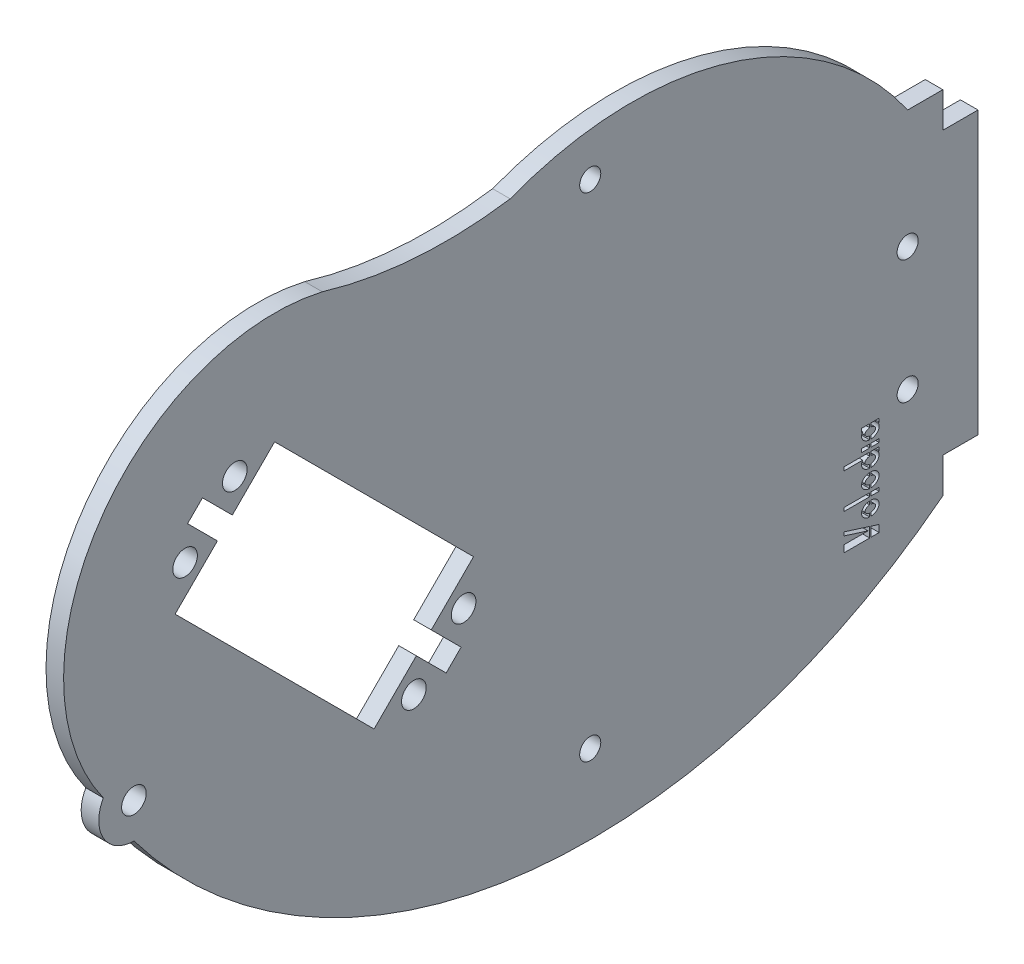
SolidWorks part; units mm, degrees
ref_plane "Alzado" through (0, 0, 0) normal (0, 0, 1) x (1, 0, 0)
ref_plane "Planta" through (0, 0, 0) normal (0, 1, 0) x (1, 0, 0)
ref_plane "Vista lateral" through (0, 0, 0) normal (1, 0, 0) x (0, 0, -1)
sketch "Croquis1" plane through (0, 0, 0) normal (1, 0, 0) x (0, 0, -1)
  line L0 (0, 0) -> (-7.0711, 7.0711) construction
  line L1 (-7.0711, 7.0711) -> (-14.1421, 0) construction
  line L2 (-14.1421, 0) -> (14.1421, -28.2843)
  line L3 (14.1421, -28.2843) -> (20.1507, -22.2757)
  line L4 (20.1507, -22.2757) -> (24.3934, -26.5183)
  line L5 (24.3934, -26.5183) -> (26.5165, -24.3952)
  line L6 (26.5165, -24.3952) -> (22.2739, -20.1525)
  line L7 (22.2739, -20.1525) -> (28.2843, -14.1421)
  line L8 (28.2843, -14.1421) -> (0, 14.1421)
  line L9 (0, 14.1421) -> (-6.0104, 8.1317)
  line L10 (-6.0104, 8.1317) -> (-10.253, 12.3744)
  line L11 (-10.253, 12.3744) -> (-12.3744, 10.253)
  line L12 (-12.3744, 10.253) -> (-8.1317, 6.0104)
  line L13 (-8.1317, 6.0104) -> (-14.1421, 0)
  line L14 (-10.253, 8.1317) -> (-12.7301, 5.6547) construction
  line L15 (-12.7301, 5.6547) -> (-10.6088, 3.5334) construction
  line L16 (-8.1317, 10.253) -> (-5.6585, 12.7263) construction
  line L17 (-5.6585, 12.7263) -> (-3.5372, 10.605) construction
  line L18 (24.3952, -22.2739) -> (26.8701, -19.799) construction
  line L19 (26.8701, -19.799) -> (24.7487, -17.6777) construction
  line L20 (22.272, -24.397) -> (19.7972, -26.8719) construction
  line L21 (19.7972, -26.8719) -> (17.6758, -24.7506) construction
  line L22 (0, 0) -> (100, 0) construction
  line L23 (85.9431, -40) -> (85.9431, 10) construction
  line L24 (95, 10) -> (90, 10)
  line L25 (85.9431, 10) -> (80.9431, 10) construction
  line L26 (80.9431, 10) -> (80.9431, -40) construction
  line L27 (80.9431, -40) -> (85.9431, -40) construction
  line L28 (80.9431, -40) -> (84.5931, -40)
  line L29 (85.9431, -40) -> (85.9431, -39)
  line L30 (85.9431, -39) -> (84.7931, -38.6357)
  line L31 (80.9431, -37.4162) -> (80.9431, -37.9162)
  line L32 (80.9431, -37.9162) -> (84.3646, -39)
  line L33 (84.3646, -39) -> (80.9431, -39)
  line L34 (95, -40) -> (95, -35) construction
  line L35 (80.9431, -39) -> (80.9431, -40)
  line L36 (83.4431, -40) -> (83.4431, 10) construction
  line L37 (83.4431, -41.8853) -> (85.9431, -41.8853) construction
  line L38 (84.6931, -41.8853) -> (84.6931, 10) construction
  line L39 (95, -40) -> (95, -35)
  line L40 (95, -35) -> (100, -35)
  line L41 (100, -35) -> (100, 5)
  line L42 (100, 5) -> (95, 5)
  line L43 (95, 10) -> (95, 5)
  line L44 (83.443, -40.8114) -> (83.943, -40.8114) construction
  line L45 (80.9431, -34.9162) -> (84.5931, -34.9162)
  line L46 (80.9431, -34.9162) -> (80.9431, -34.4162)
  line L47 (80.9431, -34.4162) -> (84.5931, -34.4162)
  line L48 (85.9431, -34.9162) -> (85.9431, -34.4162)
  line L49 (80.9431, -29.9162) -> (83.6102, -29.9162)
  line L50 (80.9431, -29.9162) -> (80.9431, -29.4162)
  line L51 (80.9431, -29.4162) -> (84.5931, -29.4162)
  line L52 (85.9431, -29.9162) -> (85.9431, -29.4162)
  line L53 (83.4431, -28.9162) -> (84.5931, -28.9162)
  line L54 (83.4431, -28.9162) -> (83.4431, -28.4162)
  line L55 (83.4431, -28.4162) -> (84.5931, -28.4162)
  line L56 (85.9431, -28.9162) -> (85.9431, -28.4162)
  line L57 (83.4431, -25.9162) -> (84.5931, -25.9162)
  line L58 (83.4431, -25.9162) -> (83.4431, -26.4162)
  line L59 (83.4431, -26.4162) -> (83.6104, -26.4162)
  line L60 (85.9431, -25.9162) -> (85.9431, -26.4162)
  line L61 (83.943, -40.8114) -> (83.943, 10) construction
  line L62 (85.7755, -26.4162) -> (85.9431, -26.4162)
  line L63 (85.7752, -29.9162) -> (85.9431, -29.9162)
  line L64 (84.7931, -25.9162) -> (85.9431, -25.9162)
  line L65 (84.7931, -26.4207) -> (84.7931, -25.9162)
  line L66 (84.5931, -37.413) -> (84.5931, -36.9117)
  line L67 (84.5931, -26.4207) -> (84.5931, -25.9162)
  line L68 (84.7931, -37.413) -> (84.7931, -36.9117)
  line L69 (84.5931, -27.913) -> (84.5931, -27.4118)
  line L70 (84.7931, -27.913) -> (84.7931, -27.4118)
  line L71 (84.7931, -28.4162) -> (85.9431, -28.4162)
  line L72 (84.7931, -28.9162) -> (85.9431, -28.9162)
  line L73 (84.5931, -28.9162) -> (84.5931, -28.4162)
  line L74 (84.7931, -28.9162) -> (84.7931, -28.4162)
  line L75 (84.7931, -29.4162) -> (85.9431, -29.4162)
  line L76 (84.5931, -29.9206) -> (84.5931, -29.4162)
  line L77 (84.7931, -29.9208) -> (84.7931, -29.4162)
  line L78 (84.5931, -31.413) -> (84.5931, -30.9117)
  line L79 (84.7931, -31.4131) -> (84.7931, -30.9118)
  line L80 (84.5931, -32.4205) -> (84.5931, -31.9193)
  line L81 (84.7931, -32.4208) -> (84.7931, -31.9195)
  line L82 (84.5931, -33.9129) -> (84.5931, -33.4116)
  line L83 (84.7931, -33.9131) -> (84.7931, -33.4119)
  line L84 (84.7931, -34.9162) -> (85.9431, -34.9162)
  line L85 (84.7931, -34.4162) -> (85.9431, -34.4162)
  line L86 (84.5931, -34.9162) -> (84.5931, -34.4162)
  line L87 (84.7931, -34.9162) -> (84.7931, -34.4162)
  line L88 (84.5931, -35.9207) -> (84.5931, -35.4194)
  line L89 (84.7931, -35.9207) -> (84.7931, -35.4194)
  line L90 (84.5931, -38.5724) -> (84.5931, -40)
  line L91 (84.7931, -38.6357) -> (84.7931, -40)
  line L92 (84.5931, -38.5724) -> (80.9431, -37.4162)
  line L93 (84.7931, -40) -> (85.9431, -40)
  circle A0 centre (-12.7301, 5.6547) radius 1.75
  circle A1 centre (-5.6585, 12.7263) radius 1.75
  circle A2 centre (26.8701, -19.799) radius 1.75
  circle A3 centre (19.7972, -26.8719) radius 1.75
  circle A4 centre (-20, -20) radius 1.75
  arc A5 (6.7853, 29.2226) -> (33.4941, 27.3116) centre (24.3979, 87.7831) ccw
  arc A6 (-24.3465, -17.5285) -> (-20, -25) centre (-20, -20) ccw
  arc A7 (-20, -25) -> (95, -40) centre (44.8712, 24.0125) ccw
  arc A8 (33.4941, 27.3116) -> (90, 10) centre (50.7819, -17.1348) cw
  circle A9 centre (90, -6.8212) radius 1.5
  arc A10 (6.7853, 29.2226) -> (-24.3465, -17.5285) centre (0, 0) ccw
  circle A11 centre (90, -24.3952) radius 1.5
  circle A12 centre (44.8712, -46.0488) radius 1.5
  circle A13 centre (44.8712, 24.0125) radius 1.5
  ellipse E0 centre (84.6931, -32.9162) end of major axis (83.4431, -32.912) minor radius 1 (84.5931, -31.9193) -> (84.5931, -33.9129) ccw
  ellipse E1 centre (84.6931, -36.4162) end of major axis (83.4431, -36.4162) minor radius 1 (84.5931, -35.4194) -> (84.5931, -37.413) ccw
  ellipse E2 centre (84.6931, -30.4162) end of major axis (85.9431, -30.418) minor radius 1 (83.6102, -29.9162) -> (84.5931, -31.413) ccw
  ellipse E3 centre (84.6931, -26.9162) end of major axis (83.4431, -26.9157) minor radius 1 (83.6104, -26.4162) -> (84.5931, -27.913) ccw
  ellipse E4 centre (84.6931, -36.4162) end of major axis (83.943, -36.4162) minor radius 0.5 (84.5931, -35.9207) -> (84.5931, -36.9117) ccw
  ellipse E5 centre (84.6931, -32.9162) end of major axis (83.943, -32.9141) minor radius 0.5 (84.5931, -32.4205) -> (84.5931, -33.4116) ccw
  ellipse E6 centre (84.6931, -30.4162) end of major axis (85.4431, -30.417) minor radius 0.5 (84.5931, -29.9206) -> (84.5931, -30.9117) ccw
  ellipse E7 centre (84.6931, -26.9162) end of major axis (83.943, -26.916) minor radius 0.5 (84.5931, -26.4207) -> (84.5931, -27.4118) ccw
  ellipse E8 centre (84.6931, -26.9162) end of major axis (83.943, -26.916) minor radius 0.5 (84.7931, -27.4118) -> (84.7931, -26.4207) ccw
  ellipse E9 centre (84.6931, -26.9162) end of major axis (83.4431, -26.9157) minor radius 1 (84.7931, -27.913) -> (85.7755, -26.4162) ccw
  ellipse E10 centre (84.6931, -30.4162) end of major axis (85.9431, -30.418) minor radius 1 (84.7931, -31.4131) -> (85.7752, -29.9162) ccw
  ellipse E11 centre (84.6931, -30.4162) end of major axis (85.4431, -30.417) minor radius 0.5 (84.7931, -30.9118) -> (84.7931, -29.9208) ccw
  ellipse E12 centre (84.6931, -32.9162) end of major axis (83.943, -32.9141) minor radius 0.5 (84.7931, -33.4119) -> (84.7931, -32.4208) ccw
  ellipse E13 centre (84.6931, -32.9162) end of major axis (83.4431, -32.912) minor radius 1 (84.7931, -33.9131) -> (84.7931, -31.9195) ccw
  ellipse E14 centre (84.6931, -36.4162) end of major axis (83.943, -36.4162) minor radius 0.5 (84.7931, -36.9117) -> (84.7931, -35.9207) ccw
  ellipse E15 centre (84.6931, -36.4162) end of major axis (83.4431, -36.4162) minor radius 1 (84.7931, -37.413) -> (84.7931, -35.4194) ccw
  dimension "D5" = 5
  dimension "D8" = 0.5
  dimension "D10" = 1
  dimension "D2" = 5
  dimension "D1" = 5
  dimension "D3" = 40
  dimension "D4" = 5
  dimension "D6" = 100
  dimension "D7" = 50
  dimension "D9" = 1
  dimension "D11" = 1
  dimension "D12" = 0.5
  dimension "D13" = 0.5
  dimension "D14" = 1
  dimension "D15" = 0.5
  dimension "D16" = 1
  dimension "D17" = 0.5
  dimension "D18" = 0.5
  dimension "D19" = 0.5
  dimension "D20" = 1
  dimension "D21" = 0.5
  dimension "D22" = 0.5
  dimension "D23" = 0.5
  dimension "D24" = 0.5
  dimension "D25" = 0.5
  dimension "D26" = 1.25
  dimension "D27" = 0.5
  dimension "D28" = 0.5
  dimension "D29" = 0.5
  dimension "D30" = 0.5
  dimension "D31" = 0.5
  dimension "D33" = 0.1
extrude "Saliente-Extruir1" add sketch "Croquis1" along normal blind 2.5
